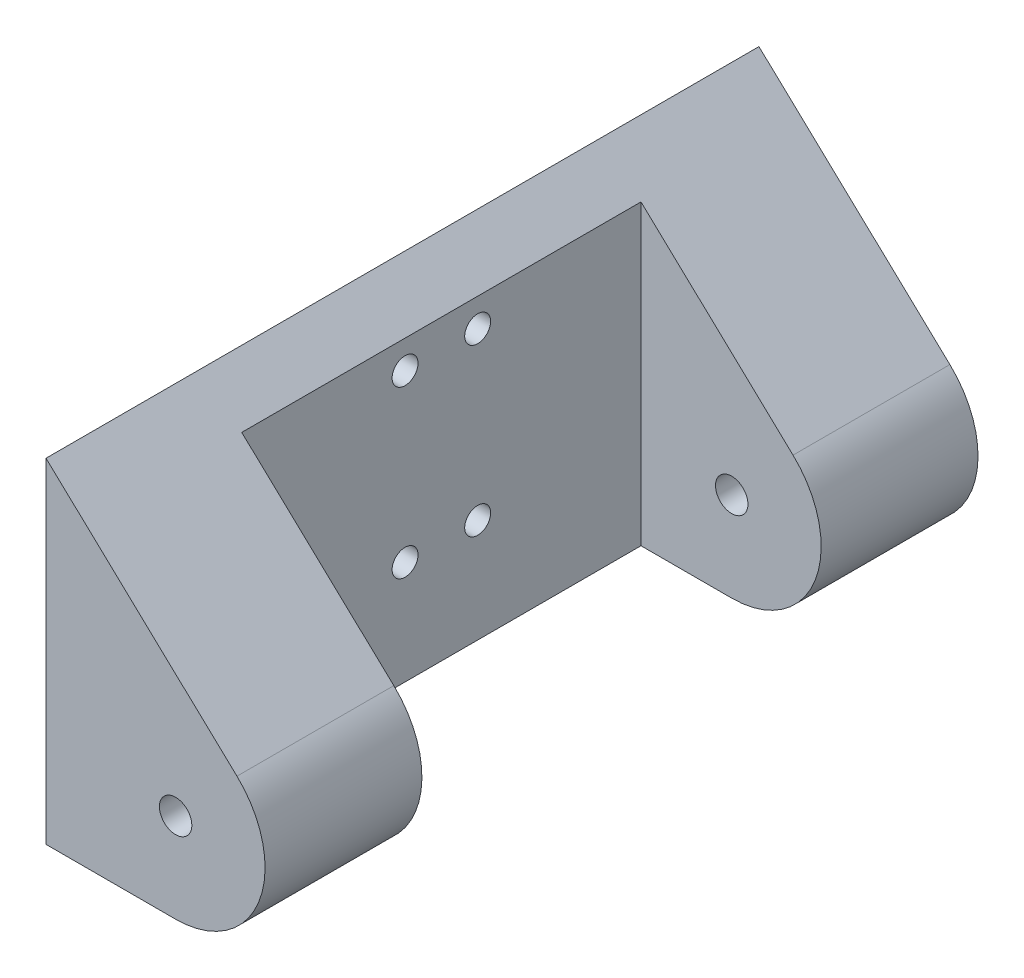
SolidWorks part; units mm, degrees
ref_plane "Front" through (0, 0, 0) normal (0, 0, 1) x (1, 0, 0)
ref_plane "Top" through (0, 0, 0) normal (0, 1, 0) x (1, 0, 0)
ref_plane "Right" through (0, 0, 0) normal (1, 0, 0) x (0, 0, -1)
sketch "Sketch1" plane through (0, 0, 0) normal (0, 0, 1) x (1, 0, 0)
  line L1 (-35, 1.5) -> (35, 1.5)
  line L2 (-35, 1.5) -> (-35, -1.5)
  line L3 (-35, -1.5) -> (35, -1.5)
  line L4 (35, 1.5) -> (35, -1.5)
  line L5 (-35, 1.5) -> (35, -1.5) construction
  line L6 (-35, -1.5) -> (35, 1.5) construction
  point P0 (0, 0)
  dimension "D1" = 70
  dimension "D2" = 3
extrude "Boss-Extrude1" add sketch "Sketch1" along normal blind 55
sketch "Sketch2" plane through (0, 1.5, 0) normal (0, 1, 0) x (1, 0, 0)
  line L0 (35, -55) -> (35, 0) construction
  line L1 (-35, 0) -> (35, 0)
  line L2 (-35, 0) -> (-35, -2.5)
  line L3 (-35, -2.5) -> (35, -2.5)
  line L4 (35, 0) -> (35, -2.5)
  line L7 (35, -55) -> (35, -52.5)
  line L8 (-35, -52.5) -> (35, -52.5)
  line L9 (-35, -55) -> (-35, -52.5)
  line L10 (-35, -55) -> (35, -55)
  dimension "D1" = 2.5
extrude "Boss-Extrude2" add sketch "Sketch2" along normal blind 22.8
sketch "Sketch5" plane through (0, 0, 55) normal (0, 0, 1) x (1, 0, 0)
  line L1 (-35, 24.3) -> (-35, -1.5) construction
  circle A0 centre (-24, 11.4) radius 3.5
  point P5 (-35, 11.4)
  dimension "D1" = 7
  dimension "D2" = 11
extrude "Cut-Extrude1" cut sketch "Sketch5" against normal blind 84.8
sketch "Sketch6" plane through (0, 24.3, 0) normal (0, 1, 0) x (1, 0, 0)
  line L0 (-35, -2.5) -> (35, -2.5) construction
  line L1 (-15, -21.7) -> (1, -21.7)
  line L2 (-15, -21.7) -> (-15, -33.3)
  line L3 (-15, -33.3) -> (1, -33.3)
  line L4 (1, -21.7) -> (1, -33.3)
  line L5 (35, -52.5) -> (-35, -52.5) construction
  line L6 (-35, -52.5) -> (-35, -2.5) construction
  line L7 (35, -52.5) -> (35, -2.5) construction
  line L8 (35, -21.7) -> (20, -21.7)
  line L9 (35, -21.7) -> (35, -33.3)
  line L10 (35, -33.3) -> (20, -33.3)
  line L11 (20, -21.7) -> (20, -33.3)
  dimension "D1" = 19.2
  dimension "D2" = 19.2
  dimension "D3" = 20
  dimension "D4" = 36
  dimension "D5" = 15
extrude "Boss-Extrude7" add sketch "Sketch6" against normal up to surface (22.8 mm away) up to face at (0, 1.5, 27.5)
sketch "Sketch7" plane through (0, 24.3, 0) normal (0, 1, 0) x (1, 0, 0)
  line L0 (1, -21.7) -> (-15, -21.7) construction
  line L1 (-15, -21.7) -> (-15, -33.3) construction
  line L2 (1, -33.3) -> (1, -21.7) construction
  line L3 (-15, -33.3) -> (1, -33.3) construction
  line L4 (35, -21.7) -> (20, -21.7) construction
  line L5 (20, -21.7) -> (20, -33.3) construction
  line L6 (35, -21.7) -> (20, -21.7) construction
  line L7 (35, -33.3) -> (35, -21.7) construction
  line L8 (20, -33.3) -> (35, -33.3) construction
  line L9 (20, -21.7) -> (20, -33.3) construction
  circle A0 centre (-12, -24.7) radius 1
  circle A1 centre (23, -30.3) radius 1
  circle A2 centre (-2, -24.7) radius 1
  circle A3 centre (-2, -30.3) radius 1
  circle A4 centre (-12, -30.3) radius 1
  circle A5 centre (23, -24.7) radius 1
  circle A6 centre (32, -24.7) radius 1
  circle A7 centre (32, -30.3) radius 1
  dimension "D1" = 2
  dimension "D2" = 2
  dimension "D3" = 3
  dimension "D4" = 3
  dimension "D5" = 3
  dimension "D6" = 3
  dimension "D7" = 3
  dimension "D8" = 3
  dimension "D9" = 3
  dimension "D10" = 3
  dimension "D11" = 3
  dimension "D12" = 3
  dimension "D13" = 3
  dimension "D14" = 3
  dimension "D15" = 3
  dimension "D16" = 3
  dimension "D17" = 3
  dimension "D18" = 3
extrude "Cut-Extrude2" cut sketch "Sketch7" against normal blind 8
sketch "Sketch8" plane through (35, 0, 0) normal (1, 0, 0) x (0, 0, -1)
  line L0 (-33.3, 1.5) -> (-33.3, 24.3) construction
  line L1 (-33.3, 24.3) -> (-21.7, 24.3) construction
  line L2 (-52.5, 1.5) -> (-33.3, 1.5) construction
  line L3 (-27.5, 24.3) -> (-27.5, 29.6427)
  circle A0 centre (-30.3, 19.3) radius 1
  circle A1 centre (-30.3, 6.5) radius 1
  circle A2 centre (-24.7, 6.5) radius 1
  circle A3 centre (-24.7, 19.3) radius 1
  dimension "D1" = 2
  dimension "D2" = 2
  dimension "D3" = 3
  dimension "D4" = 3
  dimension "D5" = 5
  dimension "D6" = 5
extrude "Cut-Extrude3" cut sketch "Sketch8" against normal blind 8 contours A3 | A0 | A2 | A1
fillet "Fillet1" radius 5 3 edges at (-15, 1.5, 27.5) (1, 1.5, 27.5) (20, 1.5, 27.5)
sketch "Sketch9" plane through (0, 0, 55) normal (0, 0, 1) x (1, 0, 0)
  line L1 (-24, 14.9) -> (-38.0844, 14.9)
  line L2 (-24, 14.9) -> (-24, 7.9)
  line L3 (-24, 7.9) -> (-38.0844, 7.9)
  line L4 (-38.0844, 14.9) -> (-38.0844, 7.9)
  circle A0 centre (-24, 11.4) radius 3.5 construction
extrude "Cut-Extrude4" cut sketch "Sketch9" against normal blind 66
sketch "Sketch10" plane through (0, 0, 55) normal (0, 0, 1) x (1, 0, 0)
  line L0 (35, 24.3) -> (49.7313, 10.4224)
  line L2 (35, 24.3) -> (35, -1.5)
  line L3 (35, -1.5) -> (45, -1.5)
  circle A0 centre (45, 5.4) radius 1.25
  arc A1 (45, -1.5) -> (49.7313, 10.4224) centre (45, 5.4) ccw
  point P10 (35, 11.4)
  dimension "D2" = 2.5
  dimension "D1" = 6
  dimension "D3" = 10
extrude "Boss-Extrude8" add sketch "Sketch10" against normal up to surface (55 mm away) up to face at (-14.3125, 11.4, 0)
sketch "Sketch11" plane through (0, -1.5, 0) normal (0, -1, 0) x (1, 0, 0)
  line L0 (35, 33.3) -> (35, 52.5) construction
  line L1 (35, 42.9) -> (54.2226, 42.9)
  line L2 (35, 42.9) -> (35, 12.1)
  line L3 (35, 12.1) -> (54.2226, 12.1)
  line L4 (54.2226, 42.9) -> (54.2226, 12.1)
extrude "Cut-Extrude5" cut sketch "Sketch11" against normal blind 35
sketch "Sketch12" plane through (35, 0, 0) normal (1, 0, 0) x (0, 0, -1)
  line L1 (-42.9, 24.3) -> (-12.1, 24.3)
  line L2 (-42.9, 24.3) -> (-42.9, -1.5)
  line L3 (-42.9, -1.5) -> (-12.1, -1.5)
  line L4 (-12.1, 24.3) -> (-12.1, -1.5)
  circle A0 centre (-30.3, 19.3) radius 1
  circle A1 centre (-30.3, 6.5) radius 1
  circle A2 centre (-24.7, 6.5) radius 1
  circle A3 centre (-24.7, 19.3) radius 1
extrude "Boss-Extrude9" add sketch "Sketch12" along normal blind 3
sketch "Sketch13" plane through (0, 0, 0) normal (0, 0, -1) x (-1, 0, 0)
  line L0 (-35, 24.3) -> (-38, 21.4739)
  line L1 (-38, 21.4739) -> (-40.5853, 23.8988)
  line L2 (-40.5853, 23.8988) -> (-37.538, 25.5113)
  line L3 (-37.538, 25.5113) -> (-35, 24.3)
extrude "Cut-Extrude6" cut sketch "Sketch13" against normal blind 96
sketch "Sketch14" plane through (0, 24.3, 0) normal (0, 1, 0) x (1, 0, 0)
  line L1 (35, -55) -> (-54.7355, -55)
  line L2 (35, -55) -> (35, 18.0878)
  line L3 (35, 18.0878) -> (-54.7355, 18.0878)
  line L4 (-54.7355, -55) -> (-54.7355, 18.0878)
extrude "Cut-Extrude7" cut sketch "Sketch14" against normal blind 96
